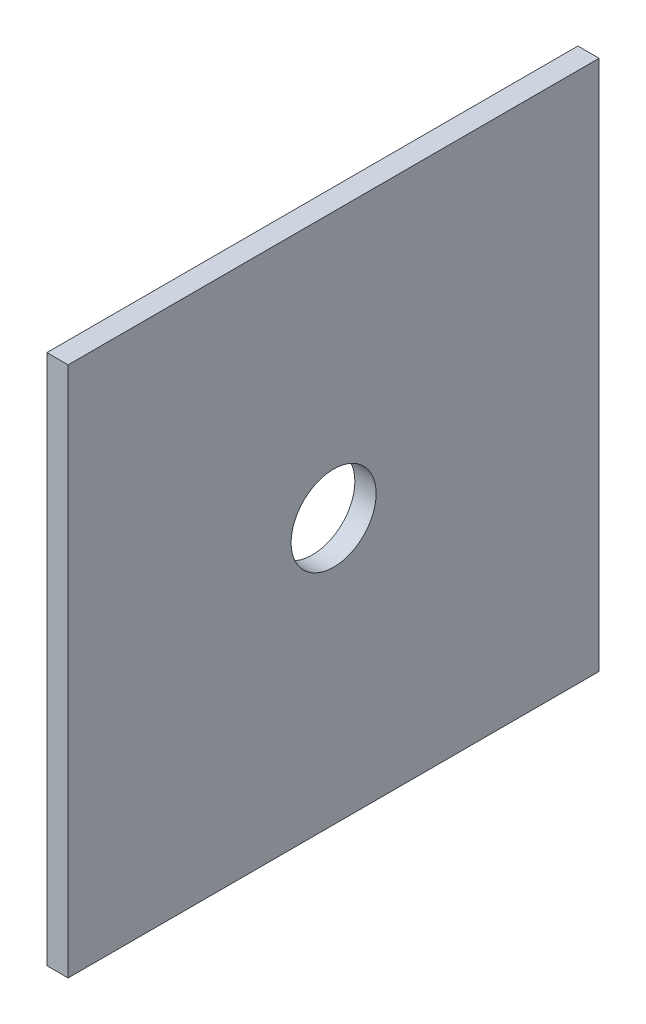
SolidWorks part; units mm, degrees
ref_plane "Front Plane" through (0, 0, 0) normal (0, 0, 1) x (1, 0, 0)
ref_plane "Top Plane" through (0, 0, 0) normal (0, 1, 0) x (1, 0, 0)
ref_plane "Right Plane" through (0, 0, 0) normal (1, 0, 0) x (0, 0, -1)
sketch "Sketch1" plane through (0, 0, 0) normal (1, 0, 0) x (0, 0, -1)
  line L1 (-50, -50) -> (50, -50)
  line L2 (-50, -50) -> (-50, 50)
  line L3 (-50, 50) -> (50, 50)
  line L4 (50, -50) -> (50, 50)
  line L5 (-50, -50) -> (50, 50) construction
  line L6 (-50, 50) -> (50, -50) construction
  circle A0 centre (0, 0) radius 8
  point P0 (0, 0)
  dimension "D1" = 100
  dimension "D2" = 100
extrude "Boss-Extrude1" add sketch "Sketch1" along normal mid plane 4
